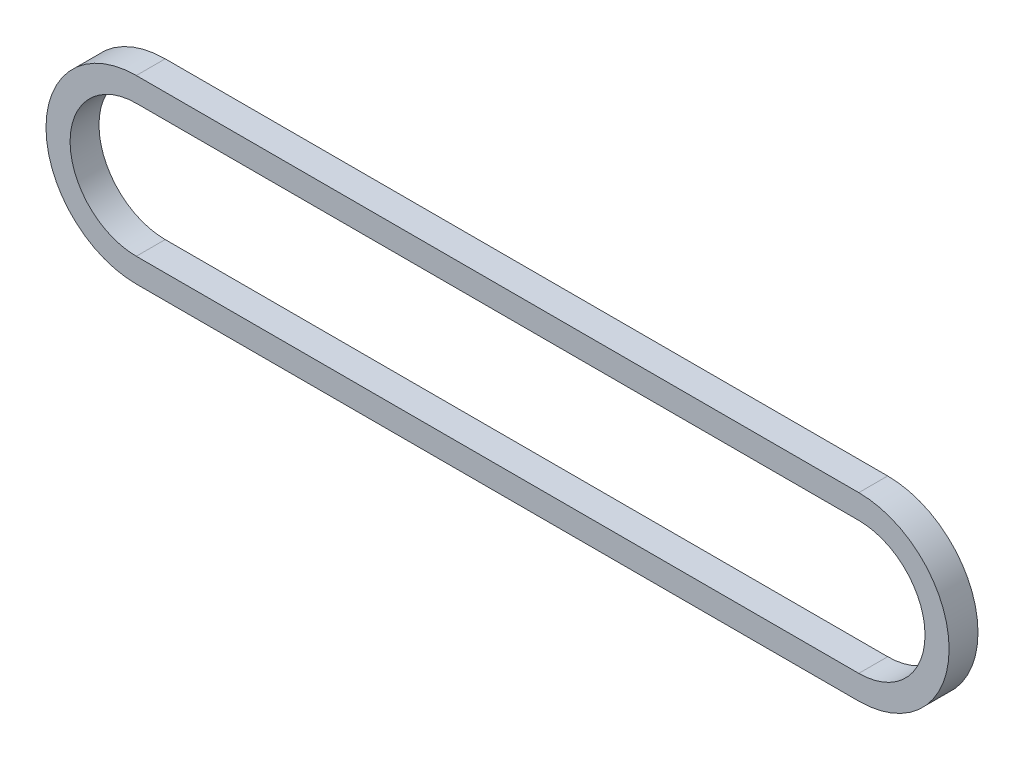
SolidWorks part; units mm, degrees
material "NEOPRENE"
ref_plane "Frontal" through (0, 0, 0) normal (0, 0, 1) x (1, 0, 0)
ref_plane "Superior" through (0, 0, 0) normal (0, 1, 0) x (1, 0, 0)
ref_plane "Direito" through (0, 0, 0) normal (1, 0, 0) x (0, 0, -1)
sketch "Esboço1" plane through (0, 0, 0) normal (0, 0, 1) x (1, 0, 0)
  line L0 (-150, 0) -> (150, 0) construction
  line L1 (-150, 37.5) -> (150, 37.5)
  line L2 (-150, -37.5) -> (150, -37.5)
  line L3 (-150, 27.5) -> (150, 27.5)
  line L4 (-150, -27.5) -> (150, -27.5)
  arc A0 (-150, 37.5) -> (-150, -37.5) centre (-150, 0) ccw
  arc A1 (150, -37.5) -> (150, 37.5) centre (150, 0) ccw
  arc A2 (150, -27.5) -> (150, 27.5) centre (150, 0) ccw
  arc A3 (-150, 27.5) -> (-150, -27.5) centre (-150, 0) ccw
  point P2 (0, 0)
  dimension "D1" = 37.5
  dimension "D2" = 300
  dimension "D3" = 10
extrude "Ressalto-extrusão1" add sketch "Esboço1" along normal mid plane 12
